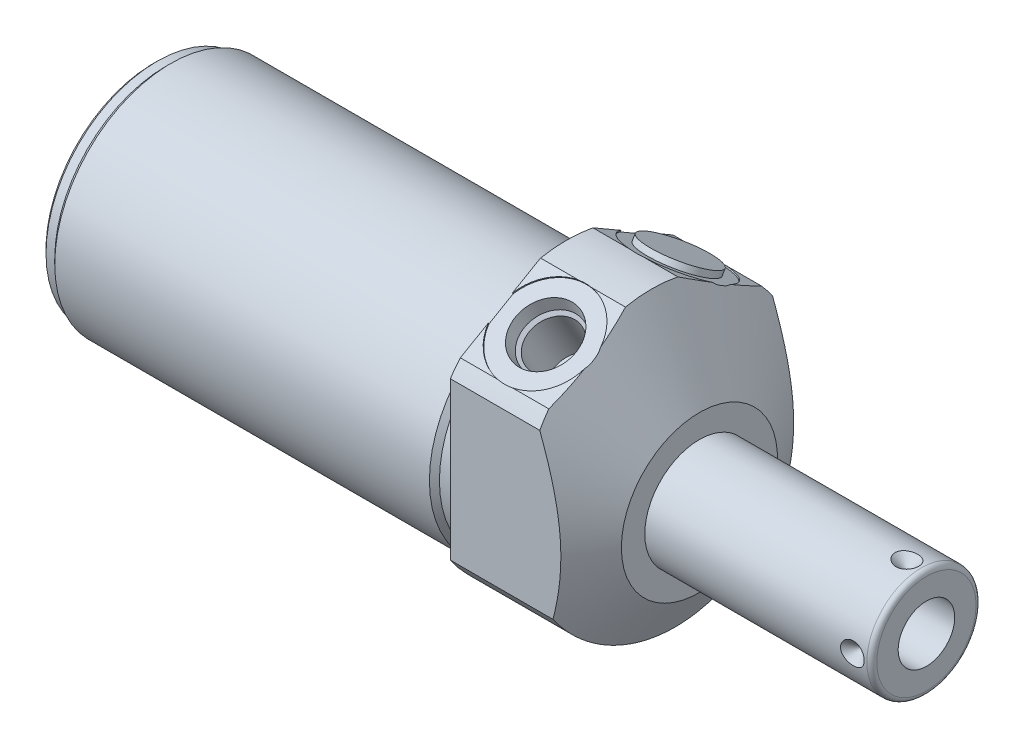
SolidWorks part; units mm, degrees
material "Alloy Steel"
ref_plane "Front Plane" through (0, 0, 0) normal (0, 0, 1) x (1, 0, 0)
ref_plane "Top Plane" through (0, 0, 0) normal (0, 1, 0) x (1, 0, 0)
ref_plane "Right Plane" through (0, 0, 0) normal (1, 0, 0) x (0, 0, -1)
ref_plane "Plane1" through (0, 0, 0) normal (1, 0, 0) x (0, 0, -1)
sketch "Sketch1" plane through (0, 0, 0) normal (1, 0, 0) x (0, 0, -1)
  circle A0 centre (0, 0) radius 28.575
  dimension "D1" = 57.15
extrude "Extrude1" add sketch "Sketch1" along normal blind 27.0002 and the other way blind 84.1248
ref_plane "Plane2" through (0, 0, 0) normal (1, 0, 0) x (0, 0, -1)
sketch "Sketch2" plane through (0, 0, 0) normal (1, 0, 0) x (0, 0, -1)
  line L0 (-25.9842, -4.191) -> (25.9842, -4.191) construction
  circle A0 centre (0, -4.191) radius 23.622
  circle A2 centre (0, 0) radius 28.575
  circle A3 centre (0, 0) radius 28.575
  dimension "D2" = 47.244
  dimension "D1" = 4.191
  dimension "D3" = 0
extrude "Cut-Extrude1" cut sketch "Sketch2" against normal up to next
ref_plane "Plane4" through (0, 0, 0) normal (-1, 0, 0) x (0, 0, 1)
sketch "Sketch4" plane through (0, 0, 0) normal (-1, 0, 0) x (0, 0, 1)
  line L0 (23.6855, -25.6662) -> (23.6855, 17.4761)
  line L1 (23.6855, 17.4761) -> (0, 31.1509)
  line L2 (-23.6855, -25.6662) -> (-23.6855, 17.4761)
  line L3 (-23.6855, 17.4761) -> (0, 31.1509)
  line L4 (0, -31.5613) -> (0, 34.1372) construction
  arc A2 (23.6855, -25.6662) -> (-23.6855, -25.6662) centre (0, 0) ccw
  dimension "D4" = 69.85
  dimension "D1" = 47.371
  dimension "D2" = 30.607
  dimension "D3" = 120
extrude "Cut-Extrude3" cut sketch "Sketch4" against normal up to next
ref_plane "Plane6" through (0, 0, 0) normal (0, 0, 1) x (1, 0, 0)
sketch "Sketch6" plane through (0, 0, 0) normal (0, 0, 1) x (1, 0, 0)
  line L0 (0.7504, 57.15) -> (27.0002, 11.684)
  line L1 (-0.5621, -4.191) -> (28.3127, -4.191) construction
  line L2 (-84.1248, -4.191) -> (0, -4.191) construction
  line L3 (27.0002, 11.684) -> (27.0002, 57.15)
  line L4 (27.0002, 57.15) -> (0.7504, 57.15)
  line L5 (27.0002, 15.9852) -> (27.0002, -15.9852) construction
  dimension "D1" = 60
  dimension "D2" = 31.75
  dimension "D3" = 122.682
revolve "Cut-Revolve2" cut sketch "Sketch6" angle 360 about L1
ref_plane "Plane7" through (9.0932, 23.1369, 13.3727) normal (1, 0, 0) x (0, 0.5, -0.866)
sketch "S2D0002" plane through (9.0932, 23.1369, 13.3727) normal (1, 0, 0) x (0, 0.5, -0.866)
  line L0 (0, 0) -> (6.1849, 0)
  line L1 (6.1849, 0) -> (5.6423, -2.5527)
  line L2 (5.6423, -2.5527) -> (4.9784, -3.2166)
  line L3 (4.9784, -3.2166) -> (4.9784, -13.462)
  line L4 (4.9784, -13.462) -> (0, -13.462)
  line L5 (0, -13.462) -> (0, 0)
  line L6 (0, -14.1351) -> (0, 0.6731) construction
  dimension "D1" = 13.462
revolve "Cut-Revolve3" cut sketch "S2D0002" angle 360 about L6
ref_plane "Plane8" through (9.0932, 23.1369, -13.3727) normal (1, 0, 0) x (0, -0.5, -0.866)
sketch "Sketch8" plane through (9.0932, 23.1369, -13.3727) normal (1, 0, 0) x (0, -0.5, -0.866)
  line L0 (0, 0) -> (6.1849, 0)
  line L1 (6.1849, 0) -> (5.6423, -2.5527)
  line L2 (5.6423, -2.5527) -> (4.9784, -3.2166)
  line L3 (4.9784, -3.2166) -> (4.9784, -13.462)
  line L4 (4.9784, -13.462) -> (0, -13.462)
  line L5 (0, -13.462) -> (0, 0)
  line L6 (0, -14.1351) -> (0, 0.6731) construction
  dimension "D1" = 13.462
revolve "Cut-Revolve4" cut sketch "Sketch8" angle 360 about L6
ref_plane "Plane10" through (0, 0, 0) normal (0, 0, 1) x (1, 0, 0)
sketch "Sketch18" plane through (0, 23.3632, 13.4887) normal (0, 0.866, 0.5) x (1, 0, 0)
  circle A0 centre (9.0932, -0.0127) radius 9.525
  dimension "D1" = 19.05
extrude "Cut-Extrude4" cut sketch "Sketch18" against normal blind 0.254
sketch "Sketch19" plane through (0, 23.3632, -13.4887) normal (0, 0.866, -0.5) x (1, 0, 0)
  circle A0 centre (9.0932, 0.0127) radius 9.525
  circle A1 centre (9.0932, 0.0127) radius 6.1849 construction
  dimension "D1" = 19.05
extrude "Cut-Extrude5" cut sketch "Sketch19" against normal blind 0.254
sketch "Sketch10" plane through (0, 0, 0) normal (0, 0, 1) x (1, 0, 0)
  line L0 (0, 19.431) -> (0, 18.415)
  line L1 (0, 18.415) -> (-3.302, 18.415)
  line L2 (-3.302, 18.415) -> (-4.318, 19.431)
  line L3 (-4.5339, -4.191) -> (0.2159, -4.191) construction
  line L4 (0, 19.431) -> (-4.318, 19.431)
  line L5 (-84.1248, -4.191) -> (0, -4.191) construction
  line L6 (0, 19.431) -> (-84.1248, 19.431) construction
  line L7 (0, 21.9392) -> (0, 18.6529) construction
  dimension "D1" = 45.212
  dimension "D2" = 45
  dimension "D3" = 3.302
revolve "Cut-Revolve6" cut sketch "Sketch10" angle 360 about L3
ref_plane "Plane12" through (0, 0, 0) normal (0, 0, 1) x (1, 0, 0)
sketch "Sketch12" plane through (0, 0, 0) normal (0, 0, 1) x (1, 0, 0)
  line L0 (-84.1248, 19.431) -> (-84.1248, 18.415)
  line L1 (-84.1248, 18.415) -> (-81.5848, 18.415)
  line L2 (-81.5848, 18.415) -> (-80.5688, 19.431)
  line L3 (-84.3026, -4.191) -> (-80.391, -4.191) construction
  line L4 (-84.1248, 19.431) -> (-80.5688, 19.431)
  line L5 (-84.1248, -4.191) -> (-4.318, -4.191) construction
  line L6 (-4.318, 19.431) -> (-84.1248, 19.431) construction
  line L7 (-84.1248, 19.431) -> (-84.1248, -27.813) construction
  dimension "D1" = 45.212
  dimension "D2" = 45
  dimension "D3" = 2.54
revolve "Cut-Revolve8" cut sketch "Sketch12" angle 360 about L3
chamfer "Chamfer1" distance 0.762 angle 45 1 edges at (-84.1248, -4.191, 22.606)
ref_plane "Plane13" through (0, 0, 0) normal (0, 0, 1) x (0, -1, 0)
sketch "Sketch13" plane through (0, 0, 0) normal (0, 0, 1) x (0, -1, 0)
  line L0 (4.191, 27.0002) -> (4.191, 73.2028)
  line L1 (4.191, 73.2028) -> (14.2875, 73.2028)
  line L2 (15.3035, 72.1868) -> (15.3035, 27.0002)
  line L3 (15.3035, 27.0002) -> (4.191, 27.0002)
  line L4 (4.191, 25.1066) -> (4.191, 66.7652) construction
  line L5 (4.191, -80.5688) -> (4.191, -4.318) construction
  line L6 (20.066, 27.0002) -> (-11.684, 27.0002) construction
  line L7 (-18.415, 0) -> (26.797, 0) construction
  arc A0 (15.3035, 72.1868) -> (14.2875, 73.2028) centre (14.2875, 72.1868) ccw
  dimension "D3" = 1.016
  dimension "D1" = 22.225
  dimension "D2" = 73.2028
revolve "Revolve1" add sketch "Sketch13" angle 360 about L4
ref_plane "Plane14" through (64.8716, -9.9441, 0) normal (0, 0, 1) x (0, -1, 0)
sketch "S2D0001" plane through (64.8716, -9.9441, 0) normal (0, 0, 1) x (0, -1, 0)
  line L0 (0, 8.3312) -> (0, -8.6868)
  line L1 (0, -8.6868) -> (-5.7531, -12.1436)
  line L2 (0, 8.3312) -> (-5.7531, 8.3312)
  line L3 (-5.7531, 8.3312) -> (-5.7531, -12.1436)
  line L4 (-5.7531, -21.4986) -> (-5.7531, 1.0237) construction
  line L5 (-5.7531, 7.3152) -> (-5.7531, -37.8714) construction
  line L6 (4.3434, 8.3312) -> (-15.8496, 8.3312) construction
  dimension "D1" = 11.5062
  dimension "D2" = 59
  dimension "D3" = 17.018
revolve "Cut-Revolve9" cut sketch "S2D0001" angle 360 about L4
ref_plane "Plane15" through (27.0002, 23.1432, -13.3617) normal (0, -0.866, 0.5) x (0, -0.5, -0.866)
sketch "Sketch15" plane through (27.0002, 23.1432, -13.3617) normal (0, -0.866, 0.5) x (0, -0.5, -0.866)
  circle A0 centre (0.0127, -17.907) radius 6.9469
  arc A1 (-2.4139, -8.6963) -> (-9.4205, -16.5878) centre (0.0127, -17.907) ccw construction
  dimension "D1" = 13.8938
extrude "Extrude2" add sketch "Sketch15" against normal blind 1.27
ref_plane "Plane16" through (60.9092, -15.3035, 0) normal (0, 0, 1) x (-1, 0, 0)
ref_plane "Plane17" through (0, -2.0955, -2.0955) normal (0, 0.7071, 0.7071) x (-1, 0, 0)
sketch "Sketch16" plane through (60.9092, 6.9215, 0) normal (0, 0, -1) x (-1, 0, 0)
  line L0 (-8.3312, 0) -> (-5.9182, 0)
  line L1 (-5.9182, 0) -> (-8.3312, -2.413)
  line L2 (-8.3312, 0) -> (-8.3312, -2.413)
  line L3 (-8.3312, -4.4865) -> (-8.3312, 0.1207) construction
  line L4 (-12.2936, -1.016) -> (-12.2936, -21.209) construction
  line L5 (33.909, 0) -> (-11.2776, 0) construction
  dimension "D1" = 45
  dimension "D2" = 3.9624
  dimension "D3" = 4.826
revolve "Cut-Revolve10" cut sketch "Sketch16" angle 360 about L3
pattern_circular "CirPattern1" count 4 over 360 about axis through (25.1066, -4.191, 0) along (-1, 0, 0) of "Cut-Revolve10"
